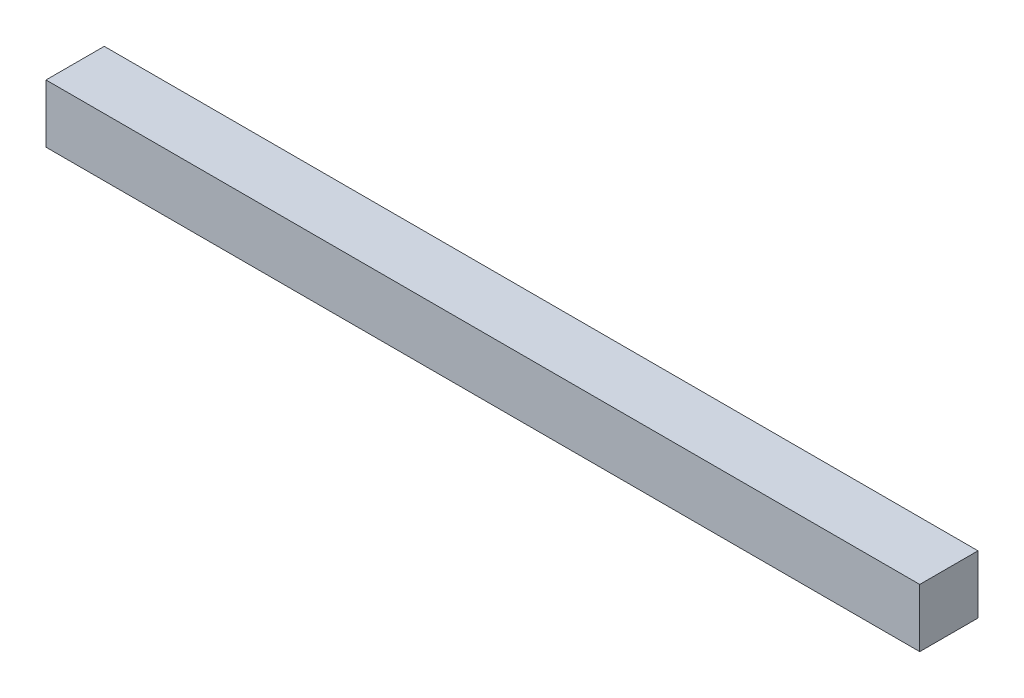
SolidWorks part; units mm, degrees
ref_plane "Front Plane" through (0, 0, 0) normal (0, 0, 1) x (1, 0, 0)
ref_plane "Top Plane" through (0, 0, 0) normal (0, 1, 0) x (1, 0, 0)
ref_plane "Right Plane" through (0, 0, 0) normal (1, 0, 0) x (0, 0, -1)
sketch "Sketch1" plane through (0, 0, 0) normal (0, 0, 1) x (1, 0, 0)
  line L1 (-75, -5) -> (75, -5)
  line L2 (-75, -5) -> (-75, 5)
  line L3 (-75, 5) -> (75, 5)
  line L4 (75, -5) -> (75, 5)
  line L5 (-75, -5) -> (75, 5) construction
  line L6 (-75, 5) -> (75, -5) construction
  point P0 (0, 0)
  dimension "D1" = 150
  dimension "D2" = 10
extrude "Boss-Extrude1" add sketch "Sketch1" along normal blind 10
